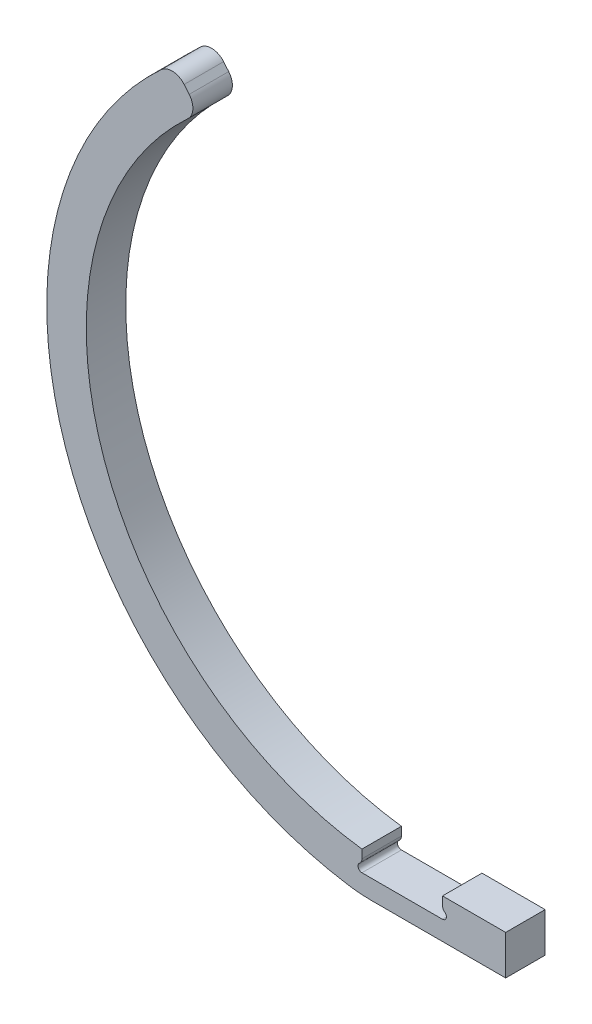
SolidWorks part; units mm, degrees
ref_plane "Front Plane" through (0, 0, 0) normal (0, 0, 1) x (1, 0, 0)
ref_plane "Top Plane" through (0, 0, 0) normal (0, 1, 0) x (1, 0, 0)
ref_plane "Right Plane" through (0, 0, 0) normal (1, 0, 0) x (0, 0, -1)
sketch "Sketch1" plane through (0, 0, 0) normal (0, 0, 1) x (1, 0, 0)
  line L0 (-6.477, -56.7818) -> (6.477, -56.7818)
  line L1 (0, -57.15) -> (0, 0) construction
  line L2 (-6.477, -53.683) -> (6.477, -53.683)
  line L3 (-6.477, -53.683) -> (6.477, -53.683) construction
  line L4 (6.477, -56.7818) -> (6.477, -53.683) construction
  line L5 (0, 0) -> (-36.7353, 43.7794) construction
  line L6 (-6.477, -53.683) -> (-6.477, -50.3854)
  line L7 (-35.0646, 41.7884) -> (-34.2474, 40.8145)
  line L8 (6.477, -53.683) -> (6.477, -50.4318)
  line L9 (16.637, -50.4318) -> (16.637, -56.7818)
  line L10 (16.637, -56.7818) -> (6.477, -56.7818)
  line L11 (6.477, -50.4318) -> (16.637, -50.4318)
  arc A0 (-38.7318, 42.0234) -> (6.477, -56.7818) centre (0, 0) ccw
  arc A1 (-34.4697, 37.316) -> (-6.477, -50.3854) centre (0, 0) ccw
  arc A2 (-34.4697, 37.316) -> (-34.2474, 40.8145) centre (-36.1931, 39.1818) ccw
  arc A3 (-36.7353, 43.7794) -> (6.477, -56.7818) centre (0, 0) ccw construction
  arc A4 (-32.6536, 38.9151) -> (5.7573, -50.4727) centre (0, 0) ccw construction
  arc A5 (-35.0646, 41.7884) -> (-38.7318, 42.0234) centre (-37.0104, 40.1557) ccw
  point P6 (0, -57.15)
  point P7 (0, -56.7818)
  dimension "D1" = 114.3
  dimension "D6" = 2.54
  dimension "D2" = 12.954
  dimension "D4" = 140
  dimension "D7" = 10.16
  dimension "D8" = 6.35
  dimension "D3" = 3.0988
  dimension "D5" = 6.35
extrude "Boss-Extrude1" add sketch "Sketch1" along normal blind 6.35 contours L7 A5 A0 L0 L4 L2 L6 A1 A2
sketch "Sketch2" plane through (0, 0, 6.35) normal (0, 0, 1) x (1, 0, 0)
  line L0 (-6.477, -53.683) -> (-6.477, -50.3854) construction
  line L1 (6.477, -53.683) -> (6.477, -50.4318) construction
  circle A0 centre (-6.477, -53.048) radius 0.635
  circle A1 centre (6.477, -53.048) radius 0.635
  dimension "D1" = 1.27
extrude "Cut-Extrude1" cut sketch "Sketch2" against normal through all
fillet "Fillet2" radius 1.016 2 edges at (-6.477, -52.413, 3.175) (6.477, -52.413, 3.175)
fillet "Fillet3" radius 25.4 1 edges at (-6.477, -56.7818, 3.175)
